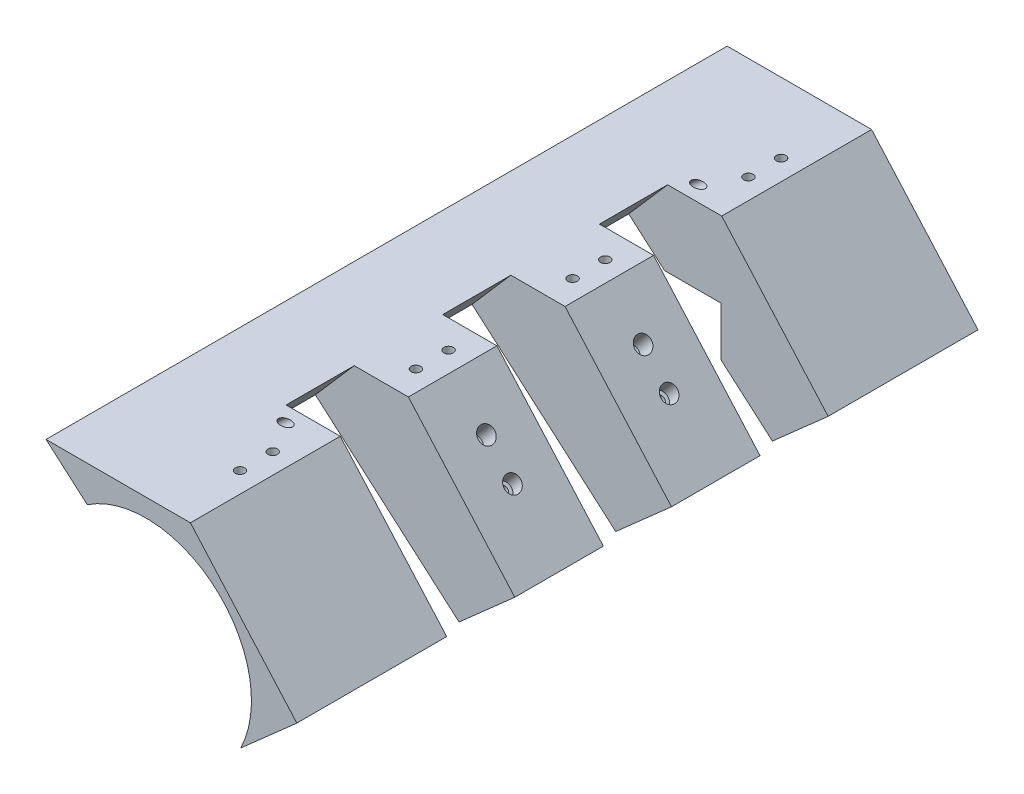
SolidWorks part; units mm, degrees
ref_plane "前视基准面" through (0, 0, 0) normal (0, 0, 1) x (1, 0, 0)
ref_plane "上视基准面" through (0, 0, 0) normal (0, 1, 0) x (1, 0, 0)
ref_plane "右视基准面" through (0, 0, 0) normal (1, 0, 0) x (0, 0, -1)
sketch "草图1" plane through (0, 0, 0) normal (0, 0, 1) x (1, 0, 0)
  line L0 (0, 0) -> (53, 0)
  line L1 (53, 0) -> (92.0571, -44.1461)
  line L2 (0, 0) -> (15.0942, -13.1212)
  line L3 (0, 0) -> (43.4296, -37.7527) construction
  line L4 (71.6023, -62.2429) -> (92.0571, -44.1461)
  line L5 (15.0942, -13.1212) -> (71.6023, -62.2429)
  dimension "D1" = 41
  dimension "D2" = 131.5
  dimension "D3" = 41
extrude "凸台-拉伸1" add sketch "草图1" along normal blind 250
sketch "草图2" plane through (0, 0, 250) normal (0, 0, 1) x (1, 0, 0)
  circle A0 centre (36.7, -45.33) radius 38.7
extrude "切除-拉伸1" cut sketch "草图2" against normal blind 42
sketch "草图3" plane through (0, 0, 208) normal (0, 0, 1) x (1, 0, 0)
  line L1 (52.7, -54.7833) -> (24.4654, -54.7833)
  line L2 (52.7, -54.7833) -> (52.7, -27.83)
  line L3 (52.7, -27.83) -> (24.4654, -27.83)
  line L4 (24.4654, -54.7833) -> (24.4654, -27.83)
extrude "切除-拉伸2" cut sketch "草图3" against normal blind 14
sketch "草图4" plane through (0, 0, 0) normal (-0.6561, -0.7547, 0) x (0.7547, -0.6561, 0)
  line L0 (195, -10.0563) -> (195, 121.1758) construction
  line L1 (0, 0) -> (183.5168, 0) construction
  line L7 (195, 55) -> (25, 55)
  line L8 (195, 55) -> (195, 80)
  line L9 (195, 80) -> (25, 80)
  line L10 (25, 55) -> (25, 80)
  line L11 (195, 112.5) -> (25, 112.5)
  line L12 (195, 112.5) -> (195, 137.5)
  line L13 (195, 137.5) -> (25, 137.5)
  line L14 (25, 112.5) -> (25, 137.5)
  line L15 (195, 170) -> (25, 170)
  line L16 (195, 170) -> (195, 195)
  line L17 (195, 195) -> (25, 195)
  line L18 (25, 170) -> (25, 195)
  dimension "D1" = 195
  dimension "D2" = 55
  dimension "D3" = 112.5
  dimension "D4" = 170
extrude "切除-拉伸3" cut sketch "草图4" against normal blind 78
ref_plane "基准面1" through (0, 0, 125) normal (0, 0, 1) x (1, 0, 0)
mirror "镜向1" about plane through (0, 0, 125) normal (0, 0, 1) of "切除-拉伸1", "切除-拉伸2"
sketch "草图5" plane through (0, 0, 0) normal (0, 1, 0) x (1, 0, 0)
  line L4 (53, -250) -> (53, -195) construction
  circle A0 centre (45.5, -212.3) radius 1.75
  circle A5 centre (45.5, -224.3) radius 1.75
  circle A6 centre (45.5, -25.7) radius 1.75
  circle A7 centre (45.5, -37.7) radius 1.75
  dimension "D1" = 12
  dimension "D3" = 7.5
sketch "草图6" plane through (0, 0, 0) normal (-0.6561, -0.7547, 0) x (0.7547, -0.6561, 0)
  circle A0 centre (72.8388, 96.25) radius 1.75
  circle A1 centre (58.5388, 96.25) radius 1.75
  circle A2 centre (72.8388, 153.75) radius 1.75
  circle A3 centre (58.5388, 153.75) radius 1.75
sketch "草图7" plane through (0, 0, 0) normal (0, 1, 0) x (1, 0, 0)
  line L0 (53, -112.5) -> (53, -80) construction
  line L1 (53, -170) -> (53, -137.5) construction
  circle A0 centre (45.5, -159.75) radius 1.75
  circle A1 centre (45.5, -147.75) radius 1.75
  circle A2 centre (45.5, -102.25) radius 1.75
  circle A3 centre (45.5, -90.25) radius 1.75
  dimension "D1" = 7.5
  dimension "D2" = 7.5
  dimension "D3" = 7.5
  dimension "D4" = 7.5
extrude "切除-拉伸5" cut sketch "草图7" against normal blind 25
extrude "切除-拉伸6" cut sketch "草图6" against normal blind 90
extrude "切除-拉伸8" cut sketch "草图5" against normal blind 10
sketch "草图9" plane through (29.7295, 26.3025, 0) normal (0.749, 0.6626, 0) x (0, 0, -1)
  line L0 (-250, 0) -> (0, 0) construction
  line L1 (-250, -35.1189) -> (-250, 0) construction
  circle A0 centre (-49.2642, -25.6019) radius 1.75
  circle A1 centre (-200.7358, -25.6019) radius 1.75
  dimension "D1" = 25.6019
  dimension "D2" = 49.2642
extrude "切除-拉伸9" cut sketch "草图9" against normal blind 124
sketch "草图10" plane through (0, -25, 0) normal (0, 1, 0) x (1, 0, 0)
  line L1 (37.9554, -84.843) -> (55.2888, -84.843)
  line L2 (37.9554, -84.843) -> (37.9554, -107.7231)
  line L3 (37.9554, -107.7231) -> (55.2888, -107.7231)
  line L4 (55.2888, -84.843) -> (55.2888, -107.7231)
extrude "切除-拉伸10" cut sketch "草图10" against normal blind 31
mirror "镜向2" about plane through (0, 0, 125) normal (0, 0, 1) of "切除-拉伸10"
ref_plane "基准面3" through (22.9621, 26.4148, 0) normal (-0.6561, -0.7547, 0) x (-0.7547, 0.6561, 0)
sketch "草图11" plane through (22.9621, 26.4148, 0) normal (-0.6561, -0.7547, 0) x (-0.7547, 0.6561, 0)
  circle A0 centre (-58.5388, -96.25) radius 3
  circle A1 centre (-72.8388, -96.25) radius 3
  circle A2 centre (-58.5388, -153.75) radius 3
  circle A3 centre (-72.8388, -153.75) radius 3
extrude "切除-拉伸11" cut sketch "草图11" along normal blind 10
sketch "草图12" plane through (0, 0, 250) normal (0, 0, 1) x (1, 0, 0)
  line L0 (77.8225, -56.7398) -> (92.0571, -44.1461)
  line L1 (71.6023, -62.2429) -> (92.0571, -44.1461) construction
  line L2 (92.0571, -44.1461) -> (81.8297, -32.5861)
  line L3 (92.0571, -44.1461) -> (53, 0) construction
sketch "草图13" plane through (0, 0, 0) normal (-0.6561, -0.7547, 0) x (0.7547, -0.6561, 0)
  line L0 (0, 250) -> (0, 0) construction
  line L1 (0, 250) -> (20.0873, 250) construction
  circle A0 centre (25.8228, 200.7358) radius 1.75
  dimension "D1" = 25.8228
  dimension "D2" = 49.2642
sketch "草图14" plane through (16.4015, 18.8677, 0) normal (0.6561, 0.7547, 0) x (0.7547, -0.6561, 0)
  line L0 (58.5388, -96.25) -> (0, -96.25) construction
  line L1 (0, -250) -> (0, 0) construction
  dimension "D1" = 58.5388
